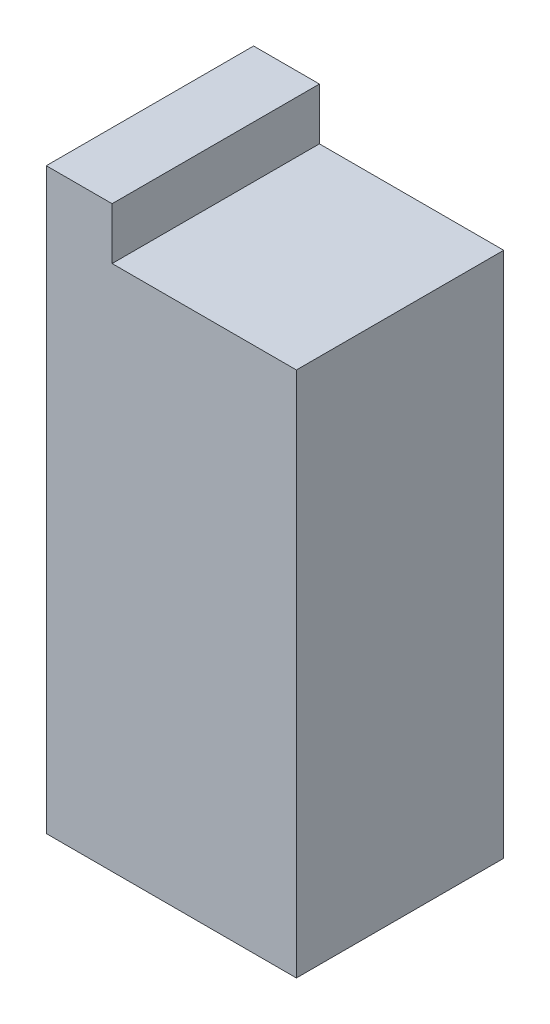
SolidWorks part; units mm, degrees
ref_plane "Front Plane" through (0, 0, 0) normal (0, 0, 1) x (1, 0, 0)
ref_plane "Top Plane" through (0, 0, 0) normal (0, 1, 0) x (1, 0, 0)
ref_plane "Right Plane" through (0, 0, 0) normal (1, 0, 0) x (0, 0, -1)
sketch "Sketch1" plane through (0, 0, 0) normal (0, 0, 1) x (1, 0, 0)
  line L0 (-8.89, -25.4) -> (-8.89, 25.4) construction
  line L1 (-8.89, -25.4) -> (8.89, -25.4)
  line L2 (-8.89, -25.4) -> (-8.89, 25.4) construction
  line L3 (-8.89, 25.4) -> (8.89, 25.4)
  line L4 (8.89, -25.4) -> (8.89, 25.4)
  line L5 (-8.89, -25.4) -> (8.89, 25.4) construction
  line L6 (-8.89, 25.4) -> (8.89, -25.4) construction
  line L7 (-8.89, -25.4) -> (-15.24, -25.4)
  line L8 (-8.89, 25.4) -> (-8.89, 30.4)
  line L9 (-8.89, 30.4) -> (-15.24, 30.4)
  line L10 (-15.24, -25.4) -> (-15.24, 30.4)
  point P0 (0, 0)
  point P10 (-8.89, 26.3761)
  dimension "D1" = 50.8
  dimension "D2" = 17.78
  dimension "D3" = 6.35
  dimension "D4" = 5
extrude "Boss-Extrude1" add sketch "Sketch1" along normal mid plane 20
equation "\"0.70i\"=0.7"
